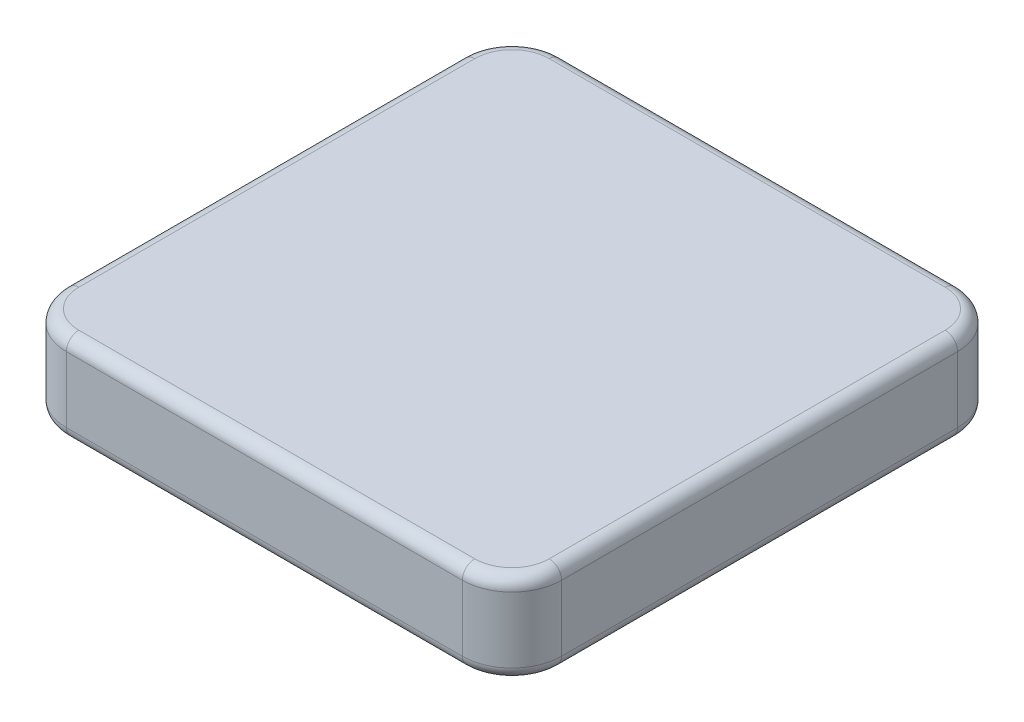
SolidWorks part; units mm, degrees
ref_plane "Front Plane" through (0, 0, 0) normal (0, 0, 1) x (1, 0, 0)
ref_plane "Top Plane" through (0, 0, 0) normal (0, 1, 0) x (1, 0, 0)
ref_plane "Right Plane" through (0, 0, 0) normal (1, 0, 0) x (0, 0, -1)
sketch "Sketch1" plane through (0, 0, 0) normal (0, 1, 0) x (1, 0, 0)
  line L1 (4, 0) -> (35.9, 0)
  line L2 (0, 4) -> (0, 35.9)
  line L3 (4, 39.9) -> (35.9, 39.9)
  line L4 (39.9, 4) -> (39.9, 35.9)
  arc A0 (0, 4) -> (4, 0) centre (4, 4) ccw
  arc A1 (35.9, 0) -> (39.9, 4) centre (35.9, 4) ccw
  arc A2 (39.9, 35.9) -> (35.9, 39.9) centre (35.9, 35.9) ccw
  arc A3 (4, 39.9) -> (0, 35.9) centre (4, 35.9) ccw
  point P7 (0, 0)
  point P14 (0, 39.9)
  dimension "D2" = 4
  dimension "D1" = 39.9
extrude "Boss-Extrude1" add sketch "Sketch1" along normal blind 7.3
fillet "Fillet1" radius 1 16 edges at (0, 7.3, -19.95) (1.1716, 7.3, -38.7284) (19.95, 7.3, -39.9) (38.7284, 7.3, -38.7284) (39.9, 7.3, -19.95) (38.7284, 7.3, -1.1716) (19.95, 7.3, 0) (1.1716, 7.3, -1.1716) (19.95, 0, 0) (38.7284, 0, -1.1716) (39.9, 0, -19.95) (38.7284, 0, -38.7284) (19.95, 0, -39.9) (1.1716, 0, -38.7284) (0, 0, -19.95) (1.1716, 0, -1.1716)
